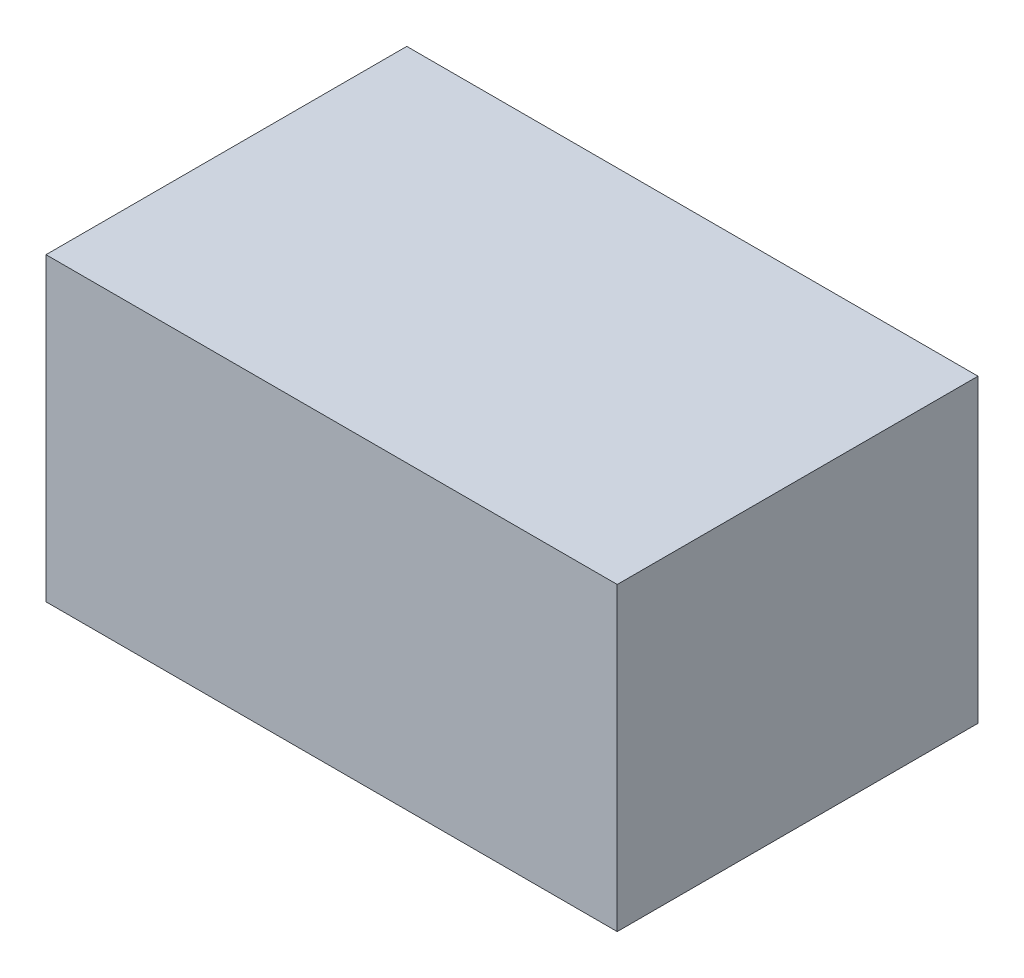
SolidWorks part; units mm, degrees
ref_plane "Front Plane" through (0, 0, 0) normal (0, 0, 1) x (1, 0, 0)
ref_plane "Top Plane" through (0, 0, 0) normal (0, 1, 0) x (1, 0, 0)
ref_plane "Right Plane" through (0, 0, 0) normal (1, 0, 0) x (0, 0, -1)
sketch "Sketch1" plane through (0, 0, 0) normal (0, 1, 0) x (1, 0, 0)
  line L1 (0, 0) -> (475, 0)
  line L2 (0, 0) -> (0, 300)
  line L3 (0, 300) -> (475, 300)
  line L4 (475, 0) -> (475, 300)
  dimension "D1" = 300
  dimension "D2" = 475
extrude "Boss-Extrude1" add sketch "Sketch1" along normal blind 250
equation "\"width\"=300"
equation "\"D1@Sketch1\"=\"width\""
equation "\"base\"= 475"
equation "\"D2@Sketch1\"=\"base\""
equation "\"height\"= 250"
equation "\"D1@Boss-Extrude1\"=\"height\""
